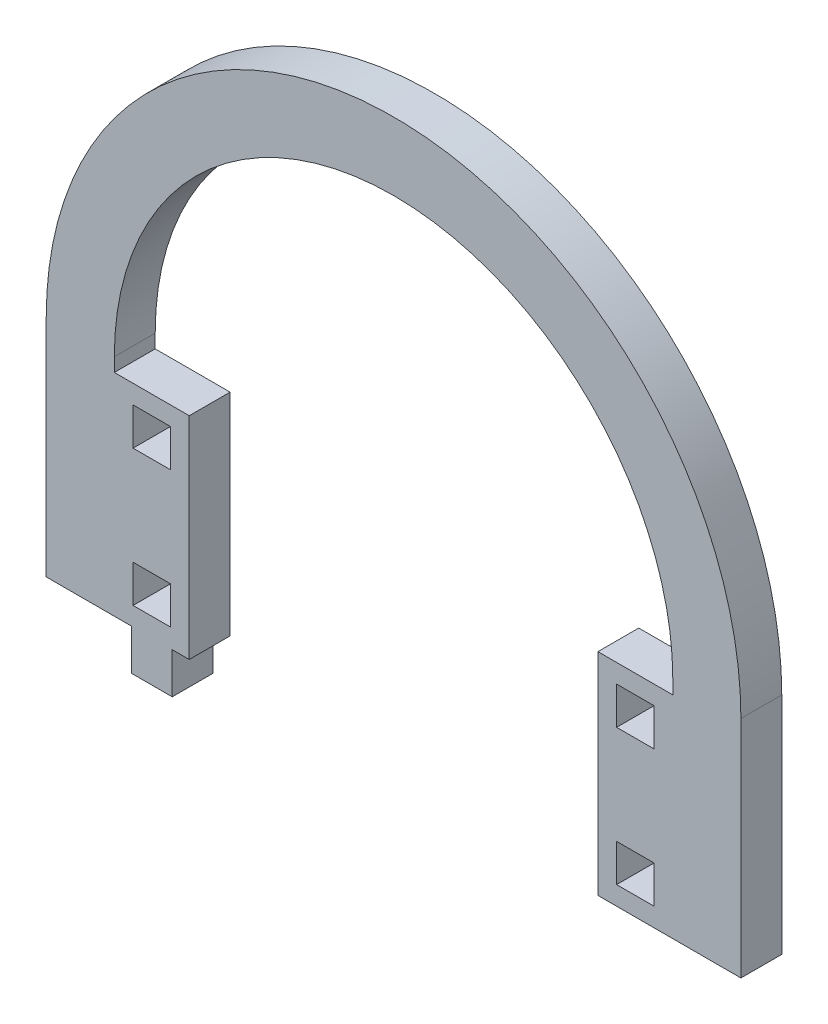
SolidWorks part; units mm, degrees
ref_plane "Front Plane" through (0, 0, 0) normal (0, 0, 1) x (1, 0, 0)
ref_plane "Top Plane" through (0, 0, 0) normal (0, 1, 0) x (1, 0, 0)
ref_plane "Right Plane" through (0, 0, 0) normal (1, 0, 0) x (0, 0, -1)
sketch "Model" plane through (0, 0, 0) normal (0, 0, 1) x (1, 0, 0)
  line L0 (3367.6843, 1328.903) -> (3367.6843, 1295.903)
  line L1 (3469.6843, 1328.903) -> (3469.6843, 1295.903)
  line L2 (3459.6843, 1328.903) -> (3459.6843, 1326.903)
  line L3 (3377.6843, 1328.903) -> (3377.6843, 1326.903)
  line L4 (3459.6843, 1295.903) -> (3469.6843, 1295.903)
  line L5 (3456.9343, 1304.153) -> (3451.4343, 1304.153)
  line L6 (3451.4343, 1304.153) -> (3451.4343, 1298.653)
  line L7 (3451.4343, 1298.653) -> (3456.9343, 1298.653)
  line L8 (3456.9343, 1298.653) -> (3456.9343, 1304.153)
  line L9 (3448.6843, 1295.903) -> (3459.6843, 1295.903)
  line L10 (3456.9343, 1324.153) -> (3451.4343, 1324.153)
  line L11 (3451.4343, 1324.153) -> (3451.4343, 1318.653)
  line L12 (3451.4343, 1318.653) -> (3456.9343, 1318.653)
  line L13 (3456.9343, 1318.653) -> (3456.9343, 1324.153)
  line L14 (3459.6843, 1326.903) -> (3448.6843, 1326.903)
  line L15 (3385.9343, 1304.153) -> (3380.4343, 1304.153)
  line L16 (3380.4343, 1304.153) -> (3380.4343, 1298.653)
  line L17 (3380.4343, 1298.653) -> (3385.9343, 1298.653)
  line L18 (3385.9343, 1298.653) -> (3385.9343, 1304.153)
  line L19 (3386.1843, 1295.903) -> (3388.6843, 1295.903)
  line L20 (3380.1843, 1295.903) -> (3380.1843, 1289.903)
  line L21 (3380.1843, 1289.903) -> (3386.1843, 1289.903)
  line L22 (3386.1843, 1289.903) -> (3386.1843, 1295.903)
  line L23 (3385.9343, 1324.153) -> (3380.4343, 1324.153)
  line L24 (3380.4343, 1324.153) -> (3380.4343, 1318.653)
  line L25 (3380.4343, 1318.653) -> (3385.9343, 1318.653)
  line L26 (3385.9343, 1318.653) -> (3385.9343, 1324.153)
  line L27 (3388.6843, 1326.903) -> (3377.6843, 1326.903)
  line L28 (3388.6843, 1326.903) -> (3388.6843, 1295.903)
  line L29 (3448.6843, 1326.903) -> (3448.6843, 1295.903)
  line L30 (3367.6843, 1295.903) -> (3380.1843, 1295.903)
  arc A0 (3469.6843, 1328.903) -> (3367.6843, 1328.903) centre (3418.6843, 1328.903) ccw
  arc A1 (3459.6843, 1328.903) -> (3377.6843, 1328.903) centre (3418.6843, 1328.903) ccw
extrude "Boss-Extrude1" add sketch "Model" along normal blind 6 contours L25 L26 L23 L24 | L17 L18 L15 L16 | L12 L13 L10 L11 | L7 L8 L5 L6 | L0 L30 L20 L21 L22 L19 L28 L27 L3 A1 L2 L14 L29 L9 L4 L1 A0
